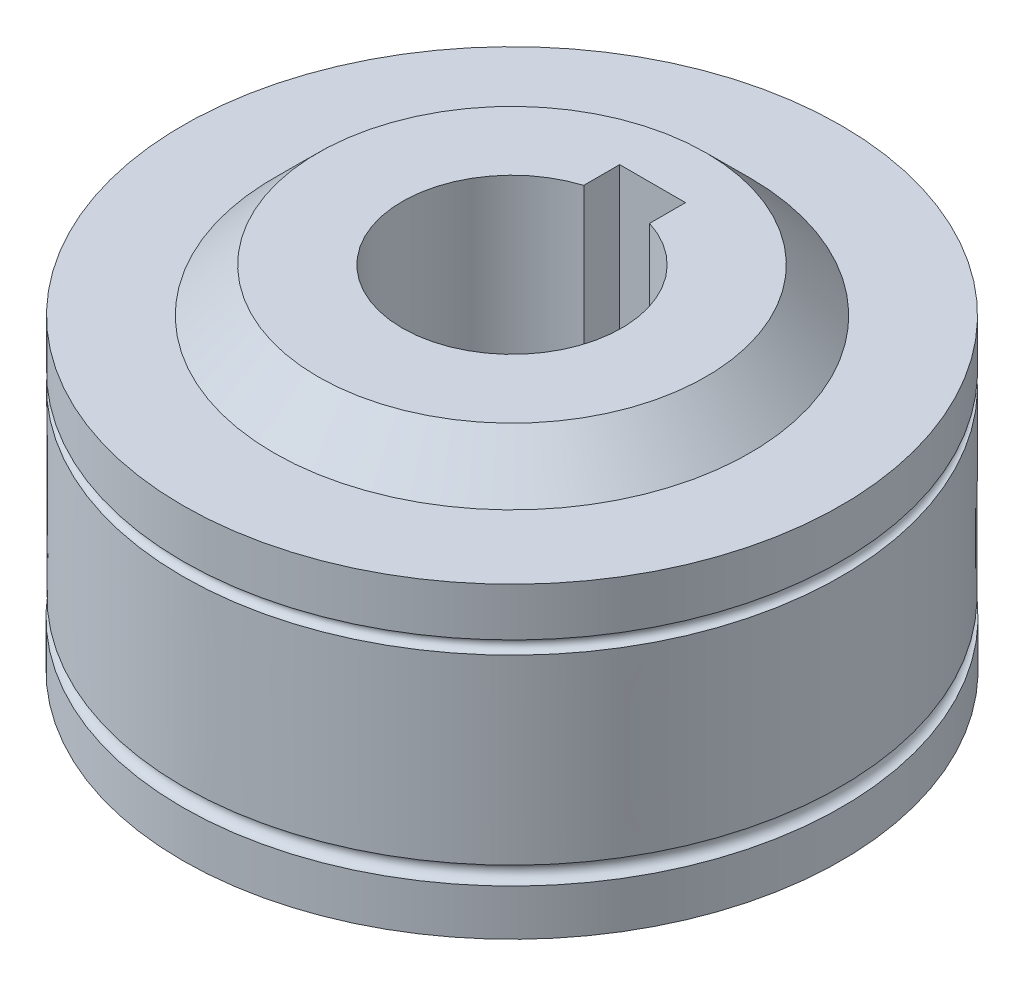
SolidWorks part; units mm, degrees
ref_plane "Спереди" through (0, 0, 0) normal (0, 0, 1) x (1, 0, 0)
ref_plane "Сверху" through (0, 0, 0) normal (0, 1, 0) x (1, 0, 0)
ref_plane "Справа" through (0, 0, 0) normal (1, 0, 0) x (0, 0, -1)
sketch "Эскиз1" plane through (0, 0, 0) normal (1, 0, 0) x (0, 0, -1)
  line L0 (0, 26.6332) -> (0, -20.8866) construction
  line L1 (15, 7) -> (15, 4.8)
  line L2 (10.8509, -7) -> (8.84, -9)
  line L3 (8.84, -9) -> (5, -9)
  line L4 (5, -9) -> (5, 9)
  line L5 (15.0173, -7) -> (15.0173, -4.8996)
  line L6 (15.0173, -7) -> (10.8509, -7)
  line L7 (15, 4.2) -> (14.9827, -4.1004)
  line L8 (15, 7) -> (10.8509, 7)
  line L9 (8.84, 9) -> (5, 9)
  line L10 (10.8509, 7) -> (8.84, 9)
  arc A0 (15, 4.8) -> (15, 4.2) centre (15, 4.5) ccw
  arc A1 (15.0173, -4.8996) -> (14.9827, -4.1004) centre (15, -4.5) cw
revolve "Повернуть1" add sketch "Эскиз1" angle 360 about L0
sketch "Эскиз2" plane through (0, 9, 0) normal (0, 1, 0) x (1, 0, 0)
  line L0 (-1.5, 4) -> (-1.5, 6.4057)
  line L1 (-1.5, 6.4057) -> (1.5, 6.4057)
  line L2 (1.5, 6.4057) -> (1.5, 4)
  line L3 (-1.5, 4) -> (1.5, 4)
extrude "Вырез-Вытянуть1" cut sketch "Эскиз2" against normal through all
